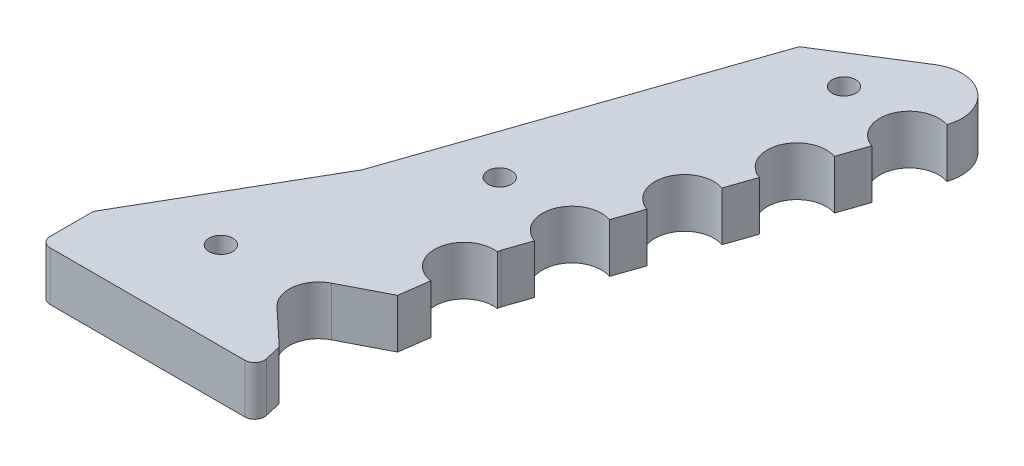
SolidWorks part; units mm, degrees
material "1060 Alloy"
ref_plane "Front" through (0, 0, 0) normal (0, 0, 1) x (1, 0, 0)
ref_plane "Top" through (0, 0, 0) normal (0, 1, 0) x (1, 0, 0)
ref_plane "Right" through (0, 0, 0) normal (1, 0, 0) x (0, 0, -1)
sketch "Sketch1" plane through (0, 0, 0) normal (0, 1, 0) x (1, 0, 0)
  line L0 (0, 0) -> (0, 30)
  line L1 (0, 30) -> (10, 47.3205)
  line L2 (10, 47.3205) -> (21.3949, 80.4137)
  line L3 (21.3949, 80.4137) -> (29.86, 85.7374)
  line L4 (35.7716, 81.049) -> (24.1579, 47.3205)
  line L5 (24.1579, 47.3205) -> (21.3949, 27.5123)
  line L6 (21.3949, 27.5123) -> (27.71, 0)
  line L7 (0, 0) -> (162.042, 0) construction
  line L8 (0, 0) -> (27.71, 0)
  arc A0 (29.86, 85.7374) -> (35.7716, 81.049) centre (31.9895, 82.3513) cw
  dimension "D4" = 4
  dimension "D1" = 20
  dimension "D2" = 35
  dimension "D3" = 10
  dimension "D5" = 30
  dimension "D6" = 60
  dimension "D7" = 71
  dimension "D8" = 27.71
  dimension "D9" = 29.86
extrude "Boss-Extrude1" add sketch "Sketch1" along normal blind 5
sketch "Sketch2" plane through (0, 5, 0) normal (0, 1, 0) x (1, 0, 0)
  line L0 (27.71, 0) -> (21.3949, 27.5123) construction
  line L1 (21.3949, 27.5123) -> (24.1579, 47.3205) construction
  line L2 (24.1579, 47.3205) -> (35.7716, 81.049) construction
  line L3 (27.71, 0) -> (21.3949, 27.5123)
  line L4 (21.3949, 27.5123) -> (24.1579, 47.3205)
  line L5 (24.1579, 47.3205) -> (35.7716, 81.049)
  line L6 (22.8684, 38.0759) -> (18.423, 35.787)
  line L7 (21.3949, 27.5123) -> (17.7455, 30.9302)
  line L8 (22.066, 24.5883) -> (18.7309, 20.8632)
  line L9 (24.4531, 14.1888) -> (19.8273, 16.0866)
  line L10 (25.1243, 11.2648) -> (21.7891, 7.5397)
  line L11 (27.5114, 0.8653) -> (22.8856, 2.7631)
  arc A0 (35.7716, 81.049) -> (33.8181, 75.3759) centre (34.7949, 78.2125) ccw
  arc A1 (32.8414, 72.5394) -> (30.888, 66.8663) centre (31.8647, 69.7028) ccw
  arc A2 (29.9113, 64.0297) -> (27.9579, 58.3566) centre (28.9346, 61.1932) ccw
  arc A3 (26.9812, 55.52) -> (25.0278, 49.8469) centre (26.0045, 52.6835) ccw
  arc A4 (24.1117, 46.9896) -> (23.2828, 41.0471) centre (23.6973, 44.0183) ccw
  arc A5 (18.423, 35.787) -> (17.7455, 30.9302) centre (19.7963, 33.1198) ccw
  arc A6 (18.7309, 20.8632) -> (19.8273, 16.0866) centre (20.966, 18.8621) ccw
  arc A7 (21.7891, 7.5397) -> (22.8856, 2.7631) centre (24.0242, 5.5386) ccw
  line M17 (21.3949, 27.5123) -> (24.1579, 47.3205)
  dimension "D1" = 3
  dimension "D7" = 3
  dimension "D2" = 9
  dimension "D3" = 18
  dimension "D4" = 27
  dimension "D5" = 36
  dimension "D6" = 5
  dimension "D8" = 3
  dimension "D9" = 3
  dimension "D10" = 10.67
  dimension "D11" = 3
  dimension "D12" = 10.67
extrude "Teeth_Cutout" cut sketch "Sketch2" against normal through all contours L5 A0 | L5 A1 | L5 A2 | L5 A3 | A4 M17 | L6 A5 L7 M17 | L8 A6 L9 L3 | L10 A7 L11 L3
fillet "Fillet2" radius 0.5 2 edges at (27.71, 2.5, 0) (27.5114, 2.5, -0.8653)
sketch "Sketch3" plane through (0, 5, 0) normal (0, 1, 0) x (1, 0, 0)
  line L0 (16.8251, 33.5343) -> (2.0405, 33.5343) construction
  line L3 (0, 9.4022) -> (23.4567, 9.4022) construction
  line L4 (0, 30) -> (0, 0) construction
  line L5 (25.1243, 11.2648) -> (21.7891, 7.5397) construction
  line L6 (10, 47.3205) -> (0, 30) construction
  line L7 (23.168, 53.6602) -> (12.1829, 53.6602) construction
  line L8 (21.3949, 80.4137) -> (10, 47.3205) construction
  line L9 (31.9583, 79.1892) -> (20.9733, 79.1892) construction
  line L10 (27.1733, 79.1892) -> (27.1733, 84.0477) construction
  line L11 (29.86, 85.7374) -> (21.3949, 80.4137) construction
  circle A0 centre (11.7284, 9.4022) radius 1.2
  arc A1 (18.423, 35.787) -> (17.7455, 30.9302) centre (19.7963, 33.1198) ccw construction
  circle A2 centre (9.4328, 33.5343) radius 1.2
  arc A3 (26.9812, 55.52) -> (25.0278, 49.8469) centre (26.0045, 52.6835) ccw construction
  arc A4 (35.7716, 81.049) -> (33.8181, 75.3759) centre (34.7949, 78.2125) ccw construction
  circle A5 centre (17.6754, 53.6602) radius 1.2
  circle A6 centre (27.1733, 79.1892) radius 1.2
  dimension "D1" = 2.4
  dimension "D2" = 6.2
extrude "Hole_Cutout" cut sketch "Sketch3" against normal through all contours A0 | A2 | A5 | A6
sketch "Sketch4" plane through (0, 5, 0) normal (0, 1, 0) x (1, 0, 0)
  line L0 (22.066, 24.5883) -> (0, 24.5883)
  line L1 (0, 30) -> (0, 0) construction
  line L2 (0, 24.5883) -> (0, 0)
  line L3 (0, 0) -> (28.6147, 0)
  line L4 (28.6147, 0) -> (28.6147, 24.5883)
  line L5 (28.6147, 24.5883) -> (22.066, 24.5883)
extrude "Cut-Extrude1" cut sketch "Sketch4" against normal through all
fillet "Fillet3" radius 1 2 edges at (22.066, 2.5, -24.5883) (0, 2.5, -24.5883)
